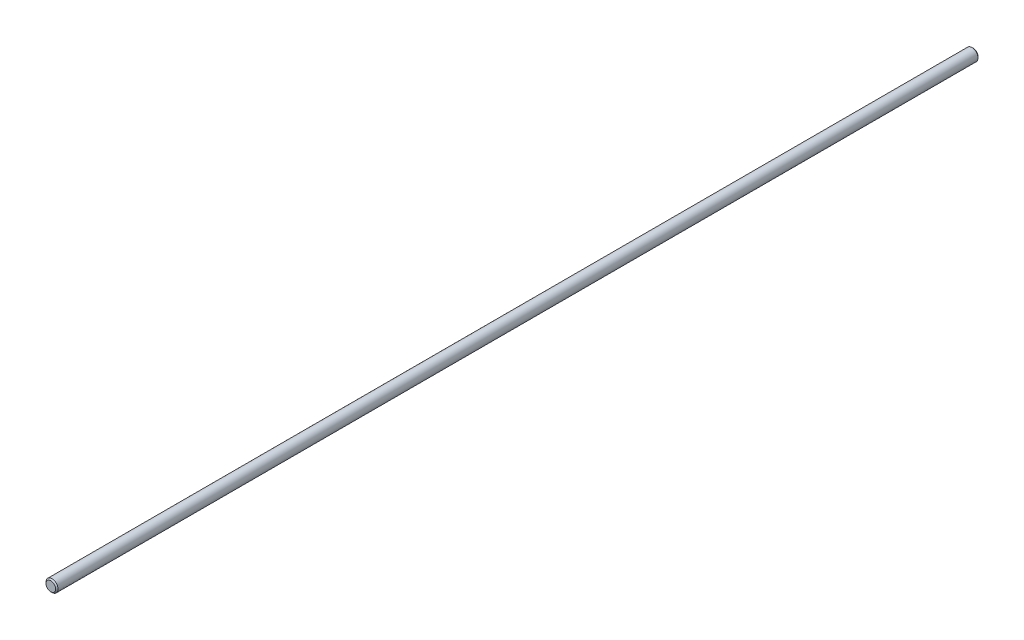
SolidWorks part; units mm, degrees
material "AISI 316 Annealed Stainless Steel Bar (SS)"
ref_plane "Front" through (0, 0, 0) normal (0, 0, 1) x (1, 0, 0)
ref_plane "Top" through (0, 0, 0) normal (0, 1, 0) x (1, 0, 0)
ref_plane "Right" through (0, 0, 0) normal (1, 0, 0) x (0, 0, -1)
sketch "Sketch1" plane through (0, 0, 0) normal (0, 0, 1) x (1, 0, 0)
  circle A0 centre (0, 0) radius 3.9688
  dimension "dia" = 7.9375
sketch "Sketch3" plane through (0, 0, 0) normal (0, 0, 1) x (1, 0, 0)
  circle A0 centre (0, 0) radius 3.9688 construction
  circle A1 centre (0, 0) radius 3.9688
extrude "Boss-Extrude1" add sketch "Sketch3" along normal mid plane 609.6
sketch "Sketch2" plane through (0, 0, 0) normal (1, 0, 0) x (0, 0, -1)
  line L0 (304.8, 3.9688) -> (-304.8, 3.9688) construction
  point P0 (-304.8, 3.9688)
  point P1 (304.8, 3.9688)
  point P2 (-288.925, 3.9688)
  point P3 (288.925, 3.9688)
  dimension "D1" = 15.875
  dimension "D2" = 15.875
chamfer "Chamfer1" distance 0.7937 angle 45 2 edges at (3.9688, 0, 304.8) (3.9688, 0, -304.8)
equation "\"D1@Chamfer1\" = \"dia@Sketch1\" / 10"
equation "\"D1@Sketch2\"=\"dia@Sketch1\"*2"
equation "\"D2@Sketch2\"=\"D1@Sketch2\""
